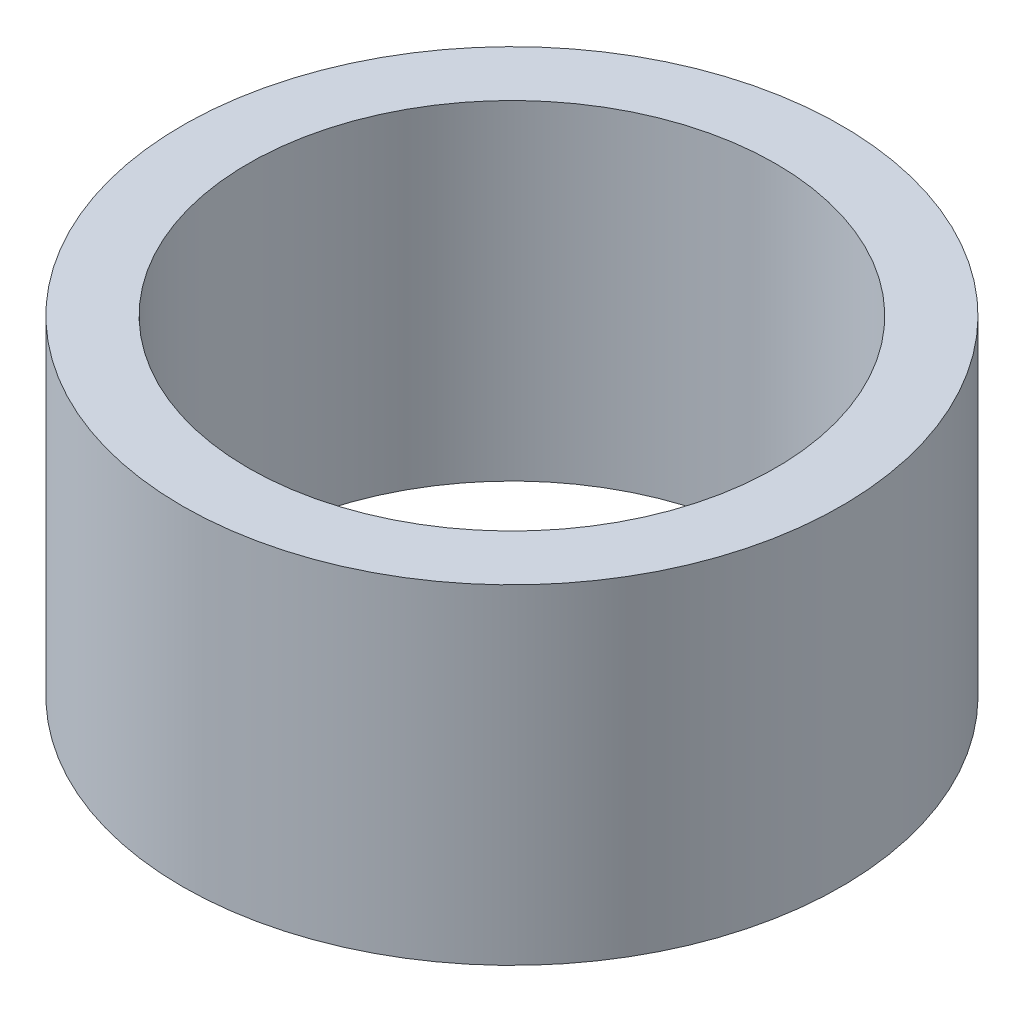
SolidWorks part; units mm, degrees
ref_plane "前视基准面" through (0, 0, 0) normal (0, 0, 1) x (1, 0, 0)
ref_plane "上视基准面" through (0, 0, 0) normal (0, 1, 0) x (1, 0, 0)
ref_plane "右视基准面" through (0, 0, 0) normal (1, 0, 0) x (0, 0, -1)
sketch "草图1" plane through (0, 0, 0) normal (0, 1, 0) x (1, 0, 0)
  circle A0 centre (0, 0) radius 20
  circle A1 centre (0, 0) radius 16
  dimension "D1" = 32
  dimension "D2" = 40
extrude "凸台-拉伸1" add sketch "草图1" along normal blind 20
